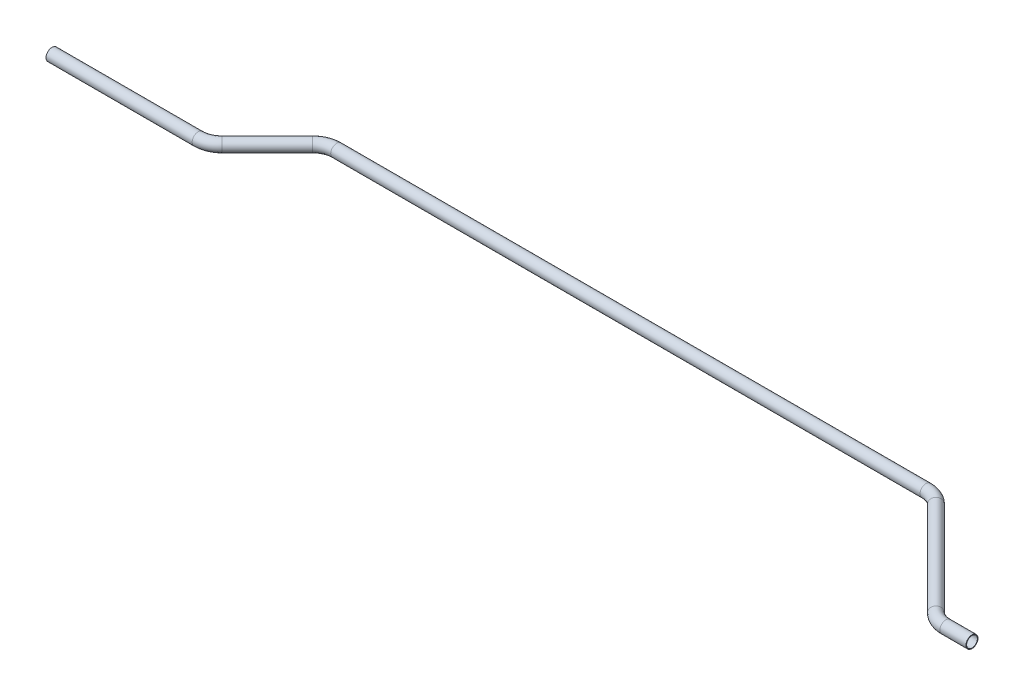
SolidWorks part; units mm, degrees
ref_plane "Front Plane" through (0, 0, 0) normal (0, 0, 1) x (1, 0, 0)
ref_plane "Top Plane" through (0, 0, 0) normal (0, 1, 0) x (1, 0, 0)
ref_plane "Right Plane" through (0, 0, 0) normal (1, 0, 0) x (0, 0, -1)
sketch "Sketch1" plane through (0, 0, 0) normal (0, 1, 0) x (1, 0, 0)
  line L0 (0, 0) -> (154.579, 0)
  line L1 (172.5395, 7.4395) -> (220.3985, 55.2985)
  line L2 (238.359, 62.738) -> (861.5175, 62.738)
  line L3 (879.478, 55.2985) -> (978.899, -44.1225)
  line L4 (996.8595, -51.562) -> (1024.4385, -51.562)
  arc A0 (978.899, -44.1225) -> (996.8595, -51.562) centre (996.8595, -26.162) ccw
  arc A1 (861.5175, 62.738) -> (879.478, 55.2985) centre (861.5175, 37.338) cw
  arc A2 (220.3985, 55.2985) -> (238.359, 62.738) centre (238.359, 37.338) cw
  arc A3 (154.579, 0) -> (172.5395, 7.4395) centre (154.579, 25.4) ccw
  point P9 (986.3385, -51.562)
  point P12 (872.0385, 62.738)
  point P15 (227.838, 62.738)
  point P18 (165.1, 0)
  dimension "D7" = 25.4
  dimension "D1" = 62.738
  dimension "D2" = 165.1
  dimension "D3" = 135
  dimension "D4" = 644.2005
  dimension "D5" = 38.1
  dimension "D6" = 114.3
ref_plane "Plane1" through (0, 0, 0) normal (1, 0, 0) x (0, 0, -1)
sketch "Sketch2" plane through (0, 0, 0) normal (1, 0, 0) x (0, 0, -1)
  circle A0 centre (0, 0) radius 6.35
  circle A1 centre (0, 0) radius 5.715
  dimension "D1" = 12.7
  dimension "D2" = 0.635
sweep "Sweep1" add profiles "Sketch2" path "Sketch1"
